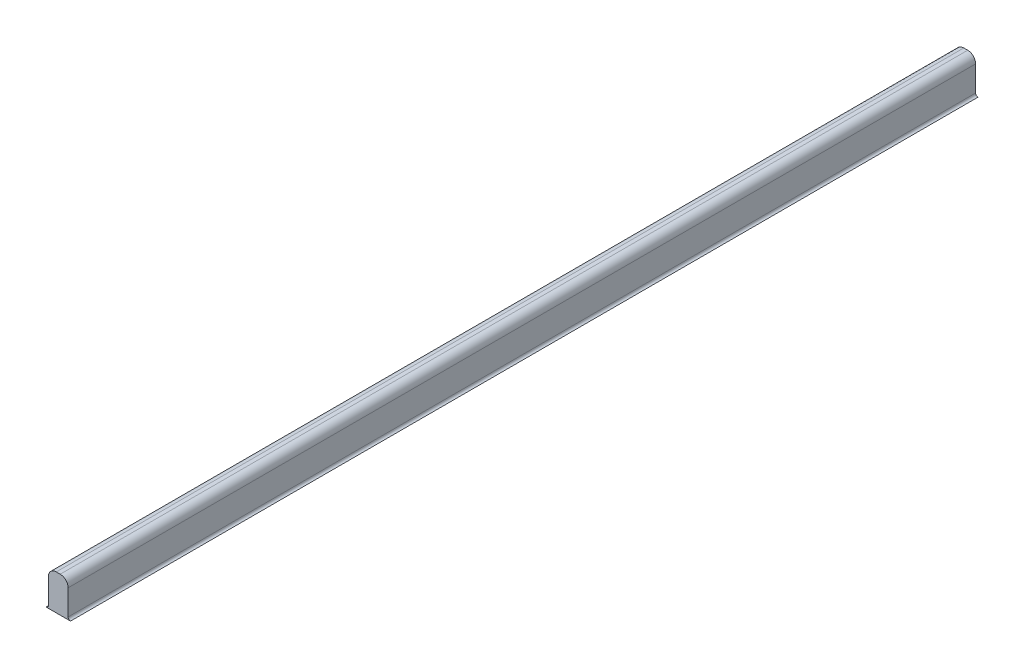
SolidWorks part; units mm, degrees
ref_plane "Plano frontal" through (0, 0, 0) normal (0, 0, 1) x (1, 0, 0)
ref_plane "Plano superior" through (0, 0, 0) normal (0, 1, 0) x (1, 0, 0)
ref_plane "Plano direito" through (0, 0, 0) normal (1, 0, 0) x (0, 0, -1)
sketch "Esboço1" plane through (0, 0, 0) normal (0, 0, 1) x (1, 0, 0)
  line L0 (-5.5, -1.5) -> (-5.8019, -1.5)
  line L1 (-4.25, -1.5) -> (-4.25, 3)
  line L2 (-5.5, -1.5) -> (-5.8019, -1.5)
  line L3 (-3, 3) -> (-5.5, 3)
  line L4 (-4.25, 3) -> (-4.25, -1.5)
  line L5 (-3, -1.5) -> (-5.5, -1.5)
  line L6 (-5.5, 3) -> (-5.5, -1.5)
  line L8 (-4.25, 3) -> (-4.25, -1.5)
  line L11 (-5.5, -1.5) -> (-5.5, -1.1981)
  line L17 (-3, -1.5) -> (-3, -1.1981)
  line L18 (-3, 3) -> (-3, -1.5)
  line L19 (-3, -1.5) -> (-2.6981, -1.5)
  line L20 (-3, -1.5) -> (-2.6981, -1.5)
  arc A0 (-5.8019, -1.5) -> (-5.5, -1.1981) centre (-5.8019, -1.1981) ccw
  arc A1 (-0.8, -1.2085) -> (-0.7998, -1.1981) centre (-1.1017, -1.1981) ccw
  arc A2 (-7.7, -1.2085) -> (-7.7002, -1.1981) centre (-7.3983, -1.1981) cw
  arc A3 (-2.6981, -1.5) -> (-3, -1.1981) centre (-2.6981, -1.1981) cw
  point P26 (0, 0)
  point P30 (0, 0)
  point P31 (0, 0)
  point P32 (-6.8864, -1.7019)
  point P33 (-6.8983, -1.6996)
  dimension "D2" = 2.5
  dimension "D4" = 4.5
extrude "Ressalto-extrusão1" add sketch "Esboço1" along normal blind 115
fillet "Filete1" radius 1 2 edges at (-3, 3, 57.5) (-5.5, 3, 57.5)
